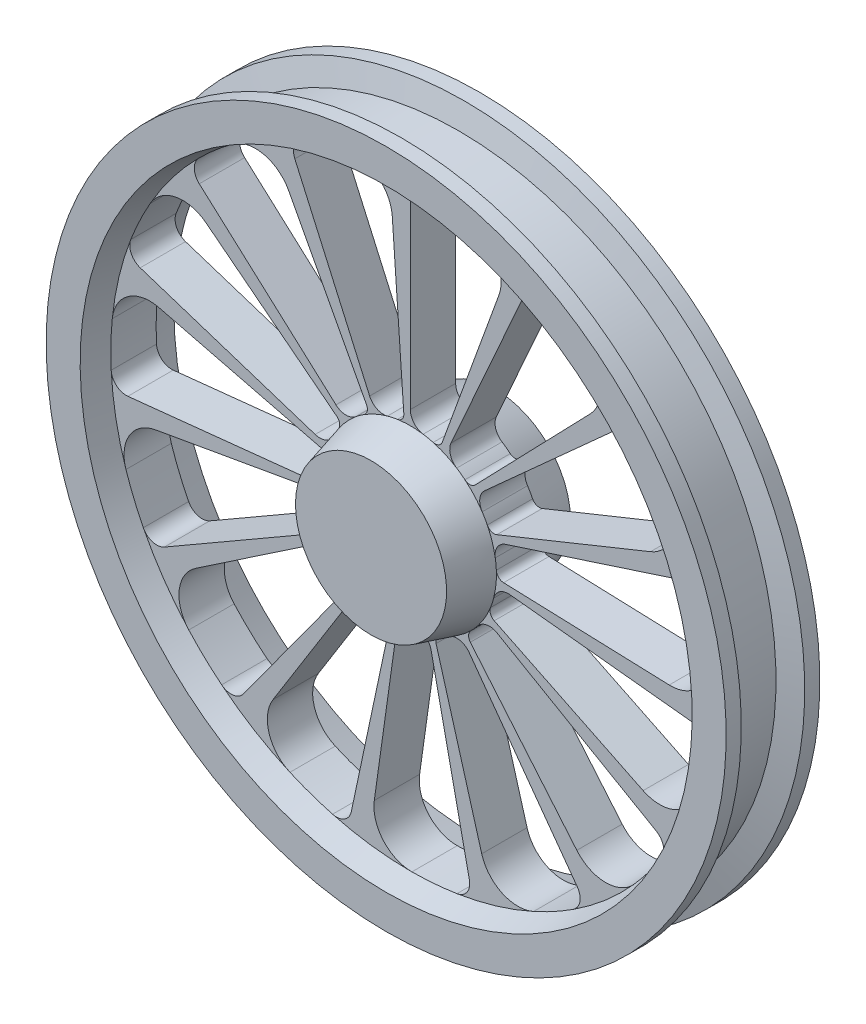
SolidWorks part; units mm, degrees
material "Stop 1060"
ref_plane "Płaszczyzna przednia" through (0, 0, 0) normal (0, 0, 1) x (1, 0, 0)
ref_plane "Płaszczyzna górna" through (0, 0, 0) normal (0, 1, 0) x (1, 0, 0)
ref_plane "Płaszczyzna prawa" through (0, 0, 0) normal (1, 0, 0) x (0, 0, -1)
sketch "Szkic1" plane through (0, 0, 0) normal (1, 0, 0) x (0, 0, -1)
  line L0 (0, 0) -> (164, 0) construction
  line L1 (0, 0) -> (0, 100)
  line L2 (0, 100) -> (52, 113.9334)
  line L3 (52, 113.9334) -> (52, 396.4256)
  line L4 (52, 396.4256) -> (20, 405)
  line L5 (20, 405) -> (20, 450)
  line L6 (20, 450) -> (40, 450)
  line L7 (40, 450) -> (48.0385, 420)
  line L8 (48.0385, 420) -> (115.9615, 420)
  line L9 (115.9615, 420) -> (124, 450)
  line L10 (124, 450) -> (144, 450)
  line L11 (144, 450) -> (144, 405)
  line L12 (144, 405) -> (112, 396.4256)
  line L13 (112, 396.4256) -> (112, 113.9334)
  line L14 (112, 113.9334) -> (164, 100)
  line L15 (164, 100) -> (164, 0)
  line L16 (0, 0) -> (164, 0)
  dimension "D1" = 100
  dimension "D2" = 60
  dimension "D3" = 75
  dimension "D4" = 75
  dimension "D5" = 30
  dimension "D7" = 75
  dimension "D8" = 20
  dimension "D9" = 45
  dimension "D10" = 75
  dimension "D11" = 75
  dimension "A" = 124
  dimension "D12" = 450
  dimension "D6" = 164
revolve "Obrót1" add sketch "Szkic1" angle 360 about L0
sketch "Szkic2" plane through (0, 0, -52) normal (0, 0, 1) x (1, 0, 0)
  line L0 (0, 132.4317) -> (0, 375.8939)
  line L1 (117.2439, 322.1251) -> (42.2495, 116.0795)
  arc A2 (21.0626, 395.8657) -> (80.3999, 388.187) centre (0, 0) cw
  arc A3 (30.2017, 109.8575) -> (17.0134, 112.6559) centre (0, 0) ccw
  arc A4 (0, 132.4317) -> (17.0134, 112.6559) centre (20, 132.4317) ccw
  arc A5 (30.2017, 109.8575) -> (42.2495, 116.0795) centre (32.8526, 119.4997) ccw
  arc A6 (80.3999, 388.187) -> (117.2439, 322.1251) centre (70.2593, 339.2261) cw
  arc A7 (0, 375.8939) -> (21.0626, 395.8657) centre (20, 375.8939) cw
  circle A8 centre (0, 0) radius 396.4256 construction
  circle A9 centre (0, 0) radius 113.9334 construction
  dimension "D2" = 20
  dimension "D3" = 50
  dimension "D4" = 20
  dimension "D5" = 10
  dimension "D1" = 20
extrude "Wytnij-wyciągnięcie1" cut sketch "Szkic2" against normal up to next (60 mm away)
pattern_circular "Szyk kołowy1" count 15 over 360 about axis through (0, 0, 0) along (0, 0, 1) of "Wytnij-wyciągnięcie1"
equation "\"A\"= 124"
equation "\"B\"= 900"
equation "\"A@Szkic1\"=\"A\""
equation "\"D12@Szkic1\"=\"B\"/2"
equation "\"D6@Szkic1\"=\"A\"+40"
